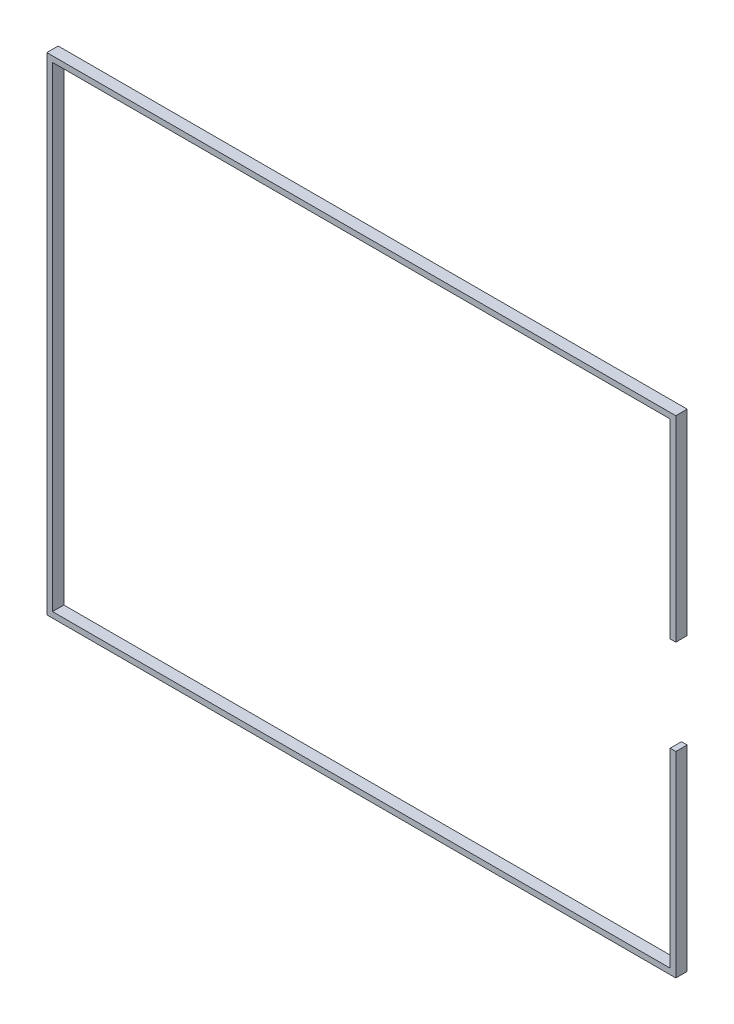
SolidWorks part; units mm, degrees
material "CA"
ref_plane "Ön Düzlem" through (0, 0, 0) normal (0, 0, 1) x (1, 0, 0)
ref_plane "Üst Düzlem" through (0, 0, 0) normal (0, 1, 0) x (1, 0, 0)
ref_plane "Sağ Düzlem" through (0, 0, 0) normal (1, 0, 0) x (0, 0, -1)
sketch "Çizim1" plane through (0, 0, 0) normal (0, 0, 1) x (1, 0, 0)
  line L0 (-35, 128.6) -> (-166.1, 35)
  line L1 (-166.1, -35) -> (166.1, -35)
  line L2 (-166.1, -35) -> (-166.1, 35)
  line L3 (-166.1, 35) -> (166.1, 35)
  line L4 (166.1, -35) -> (166.1, 35)
  line L5 (-166.1, -35) -> (166.1, 35) construction
  line L6 (-166.1, 35) -> (166.1, -35) construction
  line L7 (-35, -128.6) -> (35, -128.6)
  line L8 (-35, -128.6) -> (-35, 128.6)
  line L9 (-35, 128.6) -> (35, 128.6)
  line L10 (35, -128.6) -> (35, 128.6)
  line L11 (-35, -128.6) -> (35, 128.6) construction
  line L12 (-35, 128.6) -> (35, -128.6) construction
  line L13 (-35, -128.6) -> (-166.1, -35)
  line L14 (35, -128.6) -> (166.1, -35)
  line L15 (166.1, 35) -> (35, 128.6)
  line L16 (-148.8901, 35) -> (-35, 116.3129)
  line L17 (-35, -116.3129) -> (-148.8901, -35)
  line L18 (35, -116.3129) -> (148.8901, -35)
  line L19 (35, 116.3129) -> (148.8901, 35)
  line L20 (-35, 25) -> (-146.1, 25)
  line L21 (-146.1, 25) -> (-146.1, -25)
  line L22 (-146.1, -25) -> (-35, -25)
  line L23 (35, 25) -> (146.1, 25)
  line L24 (-25, -25) -> (25, -25)
  line L25 (-25, -25) -> (-25, 25)
  line L26 (-25, 25) -> (25, 25)
  line L27 (25, -25) -> (25, 25)
  line L28 (-25, -25) -> (25, 25) construction
  line L29 (-25, 25) -> (25, -25) construction
  line L30 (146.1, 25) -> (146.1, -25)
  line L31 (146.1, -25) -> (35, -25)
  line L32 (-25, 35) -> (-25, 108.6)
  line L33 (-25, 108.6) -> (25, 108.6)
  line L34 (25, 108.6) -> (25, 35)
  line L35 (-25, -35) -> (-25, -108.6)
  line L36 (-25, -108.6) -> (25, -108.6)
  line L37 (25, -108.6) -> (25, -35)
  line L38 (-166.1, -35) -> (-166.1, -128.6)
  line L39 (-166.1, -128.6) -> (-35, -128.6)
  line L40 (-148.8901, -35) -> (-148.8901, -116.3129)
  line L41 (-148.8901, -116.3129) -> (-35, -116.3129)
  line L42 (166.1, -35) -> (166.1, -128.6)
  line L43 (166.1, -128.6) -> (35, -128.6)
  line L44 (35, -116.3129) -> (148.8901, -116.3129)
  line L45 (148.8901, -116.3129) -> (148.8901, -35)
  line L48 (35, 128.6) -> (166.1, 128.6)
  line L49 (166.1, 128.6) -> (166.1, 35)
  line L50 (-166.1, 35) -> (-166.1, 128.6)
  line L51 (-166.1, 128.6) -> (-35, 128.6)
  line L52 (-148.8901, 35) -> (-148.8901, 116.3129)
  line L53 (-148.8901, 116.3129) -> (-35, 116.3129)
  line L54 (-25, -80) -> (25, -80)
  line L55 (-80, 25) -> (-80, -25)
  line L56 (-25, 80) -> (25, 80)
  line L57 (80, 25) -> (80, -25)
  line L58 (35, 116.3129) -> (148.8901, 116.3129)
  line L59 (148.8901, 116.3129) -> (148.8901, 35)
  point P0 (0, 0)
  point P6 (0, 0)
  point P21 (0, 0)
  dimension "D1" = 70
  dimension "D2" = 332.2
  dimension "D3" = 70
  dimension "D4" = 257.2
  dimension "D5" = 10
  dimension "D6" = 10
  dimension "D7" = 10
  dimension "D8" = 10
  dimension "D9" = 20
  dimension "D10" = 10
  dimension "D11" = 10
  dimension "D12" = 10
  dimension "D13" = 10
  dimension "D14" = 20
  dimension "D15" = 20
  dimension "D16" = 20
  dimension "D17" = 80
  dimension "D18" = 80
  dimension "D19" = 80
  dimension "D20" = 80
extrude "Yükseklik-Ekstrüzyon2" add sketch "Çizim1" against normal blind 5
sketch "Çizim2" plane through (0, 0, -5) normal (0, 0, -1) x (-1, 0, 0)
  circle A0 centre (0, 0) radius 3
  dimension "D1" = 6
extrude "Yükseklik-Ekstrüzyon3" add sketch "Çizim2" along normal blind 15
sketch "Çizim3" plane through (0, 0, 0) normal (0, 0, 1) x (1, 0, 0)
  line L4 (161.1, 0) -> (166.1, 0) construction
  line L5 (166.1, -128.6) -> (166.1, 128.6) construction
  line L6 (161.1, 25) -> (166.1, 25)
  line L7 (161.1, -25) -> (166.1, -25)
  line L8 (-161.1, -123.6) -> (161.1, -123.6)
  line L9 (161.1, -123.6) -> (161.1, 123.6)
  line L10 (161.1, 123.6) -> (-161.1, 123.6)
  line L11 (-161.1, 123.6) -> (-161.1, -123.6)
  line L12 (-161.1, -123.6) -> (161.1, -123.6)
  line L13 (161.1, -123.6) -> (161.1, 123.6)
  line L14 (161.1, 123.6) -> (-161.1, 123.6)
  line L15 (-161.1, 123.6) -> (-161.1, -123.6)
  line M23 (-166.1, -128.6) -> (166.1, -128.6)
  line M24 (166.1, -128.6) -> (166.1, 128.6)
  line M25 (166.1, 128.6) -> (-166.1, 128.6)
  line M26 (-166.1, 128.6) -> (-166.1, -128.6)
  dimension "D2" = 25
  dimension "D3" = 25
  dimension "D1" = 5
extrude "Yükseklik-Ekstrüzyon4" add sketch "Çizim3" along normal blind 6 contours L15 L14 L13 L6 L7 L12 M24 M25 M26 M23
sketch "Çizim4" plane through (0, 0, -5) normal (0, 0, -1) x (-1, 0, 0)
  line L1 (-52.5, -2.5) -> (-67.5, -2.5)
  line L2 (-52.5, -2.5) -> (-52.5, 2.5)
  line L3 (-52.5, 2.5) -> (-67.5, 2.5)
  line L4 (-67.5, -2.5) -> (-67.5, 2.5)
  line L5 (-52.5, -2.5) -> (-67.5, 2.5) construction
  line L6 (-52.5, 2.5) -> (-67.5, -2.5) construction
  line L7 (2.5, -67.5) -> (-2.5, -67.5)
  line L8 (2.5, -67.5) -> (2.5, -52.5)
  line L9 (2.5, -52.5) -> (-2.5, -52.5)
  line L10 (-2.5, -67.5) -> (-2.5, -52.5)
  line L11 (2.5, -67.5) -> (-2.5, -52.5) construction
  line L12 (2.5, -52.5) -> (-2.5, -67.5) construction
  point P0 (-60, 0)
  point P8 (0, -60)
  dimension "D1" = 5
  dimension "D2" = 15
  dimension "D3" = 60
  dimension "D4" = 5
  dimension "D5" = 15
  dimension "D6" = 60
extrude "Yükseklik-Ekstrüzyon5" add sketch "Çizim4" along normal blind 20
sketch "Çizim5" plane through (0, -2.5, 0) normal (0, -1, 0) x (1, 0, 0)
  line L0 (67.5, -5) -> (52.5, -5) construction
  line L1 (52.5, -25) -> (52.5, -5) construction
  circle A0 centre (60, -10) radius 2
  circle A1 centre (60, -19) radius 2
  dimension "D1" = 4
  dimension "D4" = 4
  dimension "D2" = 5
  dimension "D3" = 7.5
  dimension "D5" = 7.5
  dimension "D6" = 14
sketch "Çizim6" plane through (2.5, 0, 0) normal (1, 0, 0) x (0, 0, -1)
  line L0 (5, -128.6) -> (5, 128.6) construction
  line L1 (25, -67.5) -> (5, -67.5) construction
  line L2 (5, -52.5) -> (5, -67.5) construction
  circle A0 centre (10, -60) radius 2
  circle A1 centre (19, -60) radius 2
  dimension "D1" = 4
  dimension "D2" = 4
  dimension "D3" = 5
  dimension "D4" = 7.5
  dimension "D5" = 7.5
  dimension "D6" = 14
extrude "Kes-Ekstrüzyon1" cut sketch "Çizim5" against normal through all
extrude "Kes-Ekstrüzyon2" cut sketch "Çizim6" against normal through all
sketch "Çizim7" plane through (0, 0, 0) normal (0, 0, 1) x (1, 0, 0)
  line L1 (-195.7637, 149.5635) -> (198.1129, 149.5635)
  line L2 (-195.7637, 149.5635) -> (-195.7637, -153.4788)
  line L3 (-195.7637, -153.4788) -> (198.1129, -153.4788)
  line L4 (198.1129, 149.5635) -> (198.1129, -153.4788)
extrude "Kes-Ekstrüzyon3" cut sketch "Çizim7" against normal through all
sketch "Çizim8" plane through (0, 0, 6) normal (0, 0, 1) x (1, 0, 0)
  line L0 (166.1, 25) -> (166.1, 128.6) construction
  line L1 (166.1, -128.6) -> (166.1, -25) construction
  line L2 (-166.1, -128.6) -> (166.1, -128.6) construction
  line L3 (166.1, 128.6) -> (-166.1, 128.6) construction
  line L4 (-166.1, 128.6) -> (-166.1, -128.6) construction
  line L5 (166.1, 25) -> (166.1, 128.6)
  line L6 (166.1, -128.6) -> (166.1, -25)
  line L7 (-166.1, -128.6) -> (166.1, -128.6)
  line L8 (166.1, 128.6) -> (-166.1, 128.6)
  line L9 (-166.1, 128.6) -> (-166.1, -128.6)
  line L11 (-163.1, -125.6) -> (163.1, -125.6)
  line L12 (-163.1, -125.6) -> (-163.1, 125.6)
  line L13 (-163.1, 125.6) -> (163.1, 125.6)
  line L14 (163.1, -125.6) -> (163.1, 125.6)
  line L15 (-163.1, -125.6) -> (163.1, 125.6) construction
  line L16 (-163.1, 125.6) -> (163.1, -125.6) construction
  point P5 (0, 0)
  line M8 (-161.1, -123.6) -> (-161.1, 123.6)
  line M9 (-161.1, 123.6) -> (161.1, 123.6)
  line M10 (161.1, 123.6) -> (161.1, 25)
  line M11 (161.1, 25) -> (166.1, 25)
  line M17 (166.1, -25) -> (161.1, -25)
  line M18 (161.1, -25) -> (161.1, -123.6)
  line M19 (161.1, -123.6) -> (-161.1, -123.6)
  dimension "D1" = 3
  dimension "D2" = 3
extrude "Kes-Ekstrüzyon4" cut sketch "Çizim8" against normal through all contours L11 L14 L13 L12 M17 M18 M19 M8 M9 M10 M11
